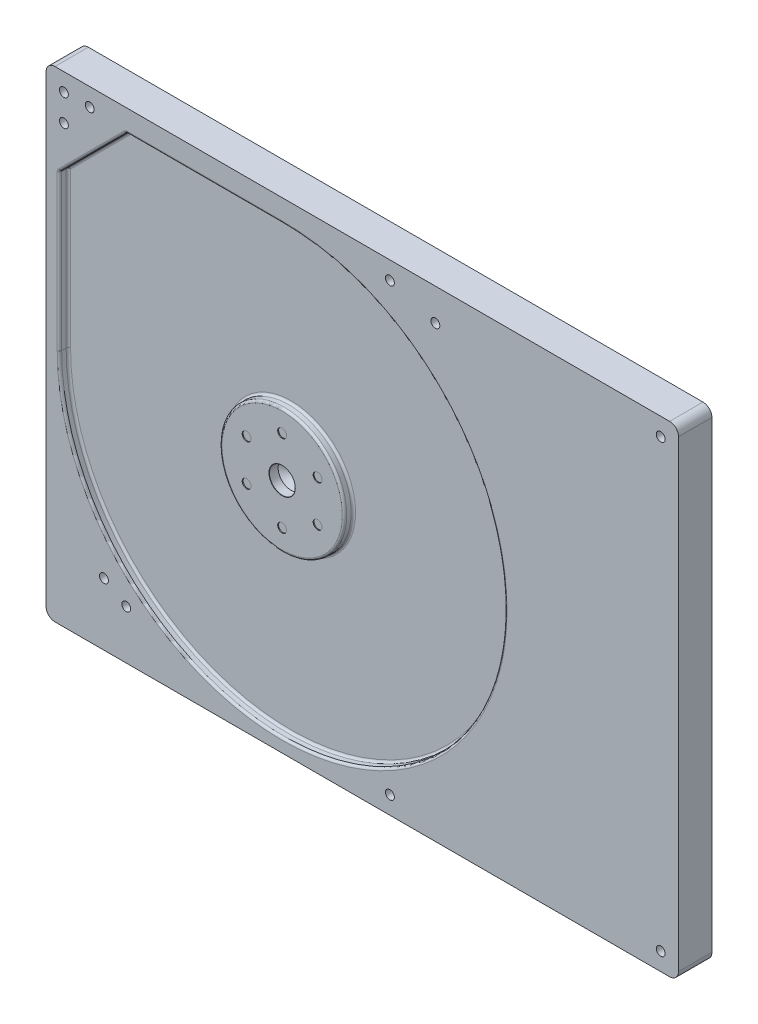
SolidWorks part; units mm, degrees
material "6061-T6 (SS)"
ref_plane "Front Plane" through (0, 0, 0) normal (0, 0, 1) x (1, 0, 0)
ref_plane "Top Plane" through (0, 0, 0) normal (0, 1, 0) x (1, 0, 0)
ref_plane "Right Plane" through (0, 0, 0) normal (1, 0, 0) x (0, 0, -1)
sketch "Sketch1" plane through (0, 0, 0) normal (0, 0, 1) x (1, 0, 0)
  line L1 (-35.5, -27) -> (35.5, -27)
  line L2 (-35.5, -27) -> (-35.5, 27)
  line L3 (-35.5, 27) -> (35.5, 27)
  line L4 (35.5, -27) -> (35.5, 27)
  line L5 (-35.5, -27) -> (35.5, 27) construction
  line L6 (-35.5, 27) -> (35.5, -27) construction
  point P0 (0, 0)
  dimension "D1" = 71
  dimension "D2" = 54
extrude "Boss-Extrude1" add sketch "Sketch1" along normal blind 3.75
fillet "Fillet1" radius 1 4 edges at (-35.5, -27, 1.875) (35.5, -27, 1.875) (35.5, 27, 1.875) (-35.5, 27, 1.875)
sketch "Sketch2" plane through (0, 0, 3.75) normal (0, 0, 1) x (1, 0, 0)
  line L0 (-35.5, 26) -> (-35.5, -26) construction
  line L1 (-34.5, -27) -> (34.5, -27) construction
  line L2 (-34, -0.5) -> (-34, 17)
  line L3 (-9, 24.5) -> (-26.5, 24.5)
  line L4 (-34, 17) -> (-26.5, 24.5)
  circle A0 centre (-9, -0.5) radius 7
  arc A1 (-34, -0.5) -> (-9, 24.5) centre (-9, -0.5) ccw
  point P0 (-9, -0.5)
  dimension "D3" = 50
  dimension "D4" = 14
  dimension "D1" = 26.5
  dimension "D2" = 26.5
  dimension "D5" = 9
extrude "Cut-Extrude1" cut sketch "Sketch2" against normal blind 1
fillet "Fillet2" radius 0.25 1 edges at (-2, -0.5, 3.75)
sketch "Sketch3" plane through (0, 0, 3.75) normal (0, 0, 1) x (1, 0, 0)
  circle A0 centre (-9, -0.5) radius 4.6 construction
  circle A1 centre (-9, 4.1) radius 0.5
  circle A2 centre (-12.9837, 1.8) radius 0.5
  circle A3 centre (-12.9837, -2.8) radius 0.5
  circle A4 centre (-9, -5.1) radius 0.5
  circle A5 centre (-5.0163, -2.8) radius 0.5
  circle A6 centre (-5.0163, 1.8) radius 0.5
  point P17 (-9, -0.5)
  dimension "D1" = 9.2
  dimension "D2" = 1
  dimension "D3" = 6
extrude "Cut-Extrude2" cut sketch "Sketch3" against normal blind 0.1
fillet "Fillet3" radius 0.25 11 edges at (8.6777, -18.1777, 3.75) (-34, 8.25, 3.75) (-34, 17, 3.25) (-30.25, 20.75, 3.75) (-26.5, 24.5, 3.25) (-17.75, 24.5, 3.75) (-34, 8.25, 2.75) (-30.25, 20.75, 2.75) (-17.75, 24.5, 2.75) (8.6777, -18.1777, 2.75) (-2, -0.5, 2.75)
hole_wizard "M2.5 Clearance Hole1" positions "Sketch5" profile "Sketch6" hole size "M2.5" standard "ANSI Metric"
sketch "Sketch5" plane through (0, 0, 3.75) normal (0, 0, 1) x (1, 0, 0)
  point P0 (-9, -0.5)
sketch "Sketch6" plane through (-9, -0.5, 3.75) normal (1, 0, 0) x (0, -1, 0)
  line L0 (0, 0) -> (0, 1.8712)
  line L1 (0, 1.8712) -> (1.45, 1)
  line L2 (1.45, 1) -> (1.45, 0.025)
  line L3 (1.45, 0.025) -> (1.475, 0)
  line L5 (1.475, 0) -> (0, 0)
  line L6 (-1.45, 0.025) -> (-1.475, 0) construction
  line L10 (0, 1.8712) -> (-1.45, 1) construction
  line L11 (0, -6.35) -> (0, 107.95) construction
  dimension "Hole Dia." = 2.9
  dimension "Hole Depth" = 1
  dimension "Near C'Sink Dia." = 2.95
  dimension "Near C'Sink Angle" = 90
  dimension "Drill Angle" = 118
sketch "Sketch7" plane through (0, 0, 3.75) normal (0, 0, 1) x (1, 0, 0)
  line L0 (-35.5, 26) -> (-35.5, -26) construction
  line L1 (34.5, 27) -> (-34.5, 27) construction
  line L2 (33.5, 27) -> (33.5, -27) construction
  line L3 (-33.5, 25) -> (-33.5, 22) construction
  line L4 (-35.5, 25) -> (35.5, 25) construction
  line L5 (35.5, -26) -> (35.5, 26) construction
  line L6 (-34.5, -27) -> (34.5, -27) construction
  line L7 (35.5, -25) -> (-35.5, -25) construction
  line L8 (3.1, 25) -> (3.1, -25) construction
  point P0 (-33.5, 25)
  point P1 (-30.6, 25)
  point P6 (3.1, 25)
  point P10 (-33.5, 22)
  point P11 (8.2, 23.4)
  point P19 (33.5, -25)
  point P22 (3.1, -25)
  point P23 (33.5, 25)
  point P26 (-29, -20)
  point P27 (-26.5, -21.5)
  dimension "D1" = 2
  dimension "D2" = 4.9
  dimension "D3" = 2
  dimension "D4" = 5
  dimension "D5" = 2
  dimension "D6" = 38.6
  dimension "D7" = 3.6
  dimension "D8" = 43.7
  dimension "D9" = 2
  dimension "D10" = 2
  dimension "D11" = 6.5
  dimension "D12" = 9
  dimension "D13" = 7
  dimension "D14" = 5.5
hole_wizard "M1.6 Clearance Hole1" positions "Sketch8" profile "Sketch9" hole size "M1.6" standard "ANSI Metric" end condition through all
sketch "Sketch8" plane through (0, 0, 3.75) normal (0, 0, 1) x (1, 0, 0)
  point P0 (-169.7807, 67.4579)
  point P2 (-33.5, 22)
  point P5 (-30.6, 25)
  point P8 (3.1, 25)
  point P11 (33.5, 25)
  point P14 (8.2, 23.4)
  point P17 (33.5, -25)
  point P20 (3.1, -25)
  point P23 (-26.5, -21.5)
  point P26 (-29, -20)
  point P29 (-33.5, 25)
sketch "Sketch9" plane through (-169.7807, 67.4579, 3.75) normal (1, 0, 0) x (0, -1, 0)
  line L0 (0, 0) -> (0, 3.75)
  line L1 (0, 3.75) -> (0.5, 3.75)
  line L2 (0.5, 3.75) -> (0.5, 0)
  line L5 (0.5, 0) -> (0, 0)
  line L11 (0, -6.35) -> (0, 107.95) construction
  dimension "Thru Hole Dia." = 1
  dimension "Thru Hole Depth" = 3.75
sketch "HDD Mounting Screw Pattern" plane through (0, 0, 3.75) normal (0, 0, 1) x (1, 0, 0)
  point P0 (-33.5, 25)
  point P1 (3.1, 25)
  point P3 (8.2, 23.4)
  point P5 (33.5, 25)
  point P7 (33.5, -25)
  point P9 (3.1, -25)
  point P11 (0, 0)
